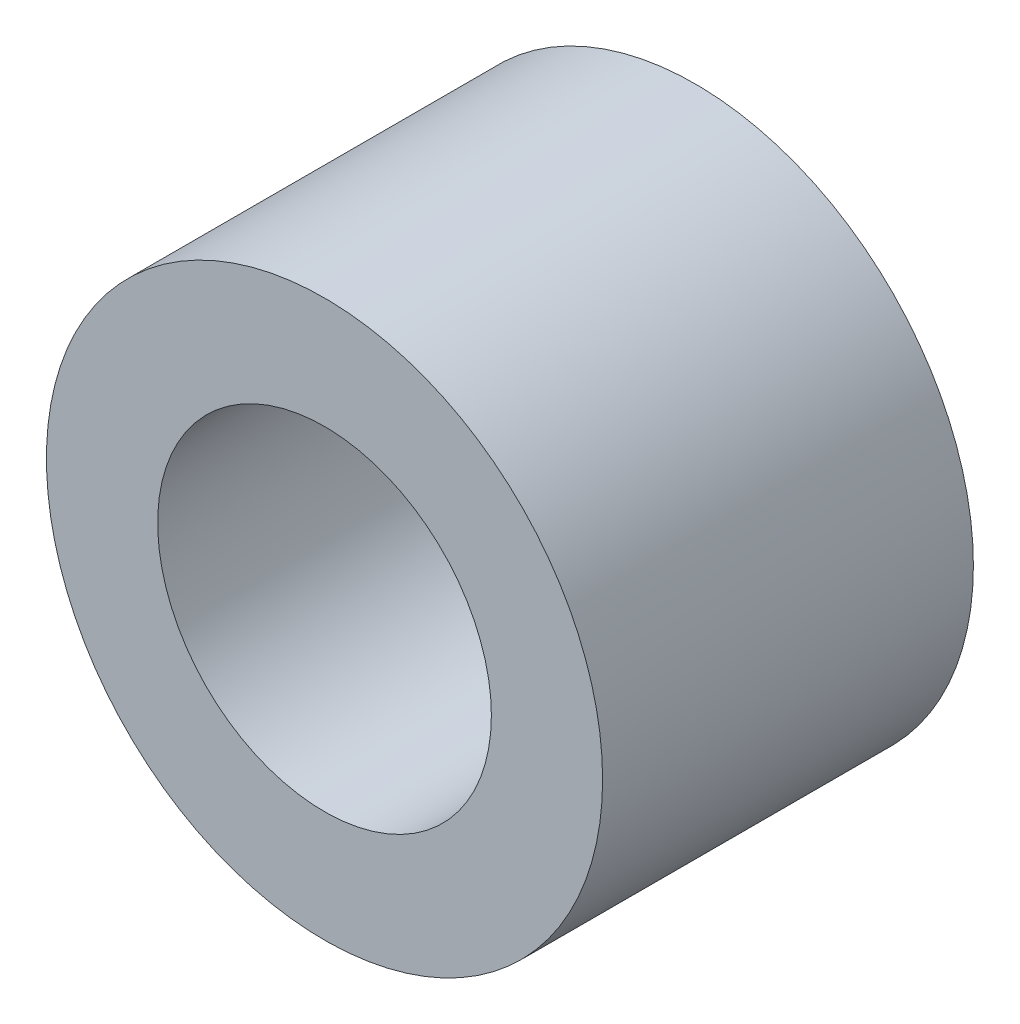
SolidWorks part; units mm, degrees
ref_plane "Front Plane" through (0, 0, 0) normal (0, 0, 1) x (1, 0, 0)
ref_plane "Top Plane" through (0, 0, 0) normal (0, 1, 0) x (1, 0, 0)
ref_plane "Right Plane" through (0, 0, 0) normal (1, 0, 0) x (0, 0, -1)
sketch "Sketch1" plane through (0, 0, 0) normal (0, 0, 1) x (1, 0, 0)
  circle A0 centre (0, 0) radius 2.25
  circle A1 centre (0, 0) radius 1.35
  dimension "OD" = 4.5
  dimension "ID" = 2.7
extrude "Extrude1" add sketch "Sketch1" along normal mid plane 3
sketch "Sketch2" plane through (0, 0, 0) normal (1, 0, 0) x (0, 0, -1)
  line L0 (-1.5, -1.35) -> (1.5, -1.35) construction
  line L3 (1.5, 1.35) -> (-1.5, 1.35) construction
  line L5 (-1.5, -1.35) -> (1.5, -1.35)
  line L6 (1.5, 1.35) -> (-1.5, 1.35)
sketch "Sketch4" plane through (0, 0, 1.5) normal (0, 0, 1) x (1, 0, 0)
  line L0 (0, 0) -> (-0.9546, 0.9546)
  line L1 (0, -1.1) -> (0, 1.1) construction
  circle A0 centre (0, 0) radius 1.35 construction
  dimension "D1" = 45
